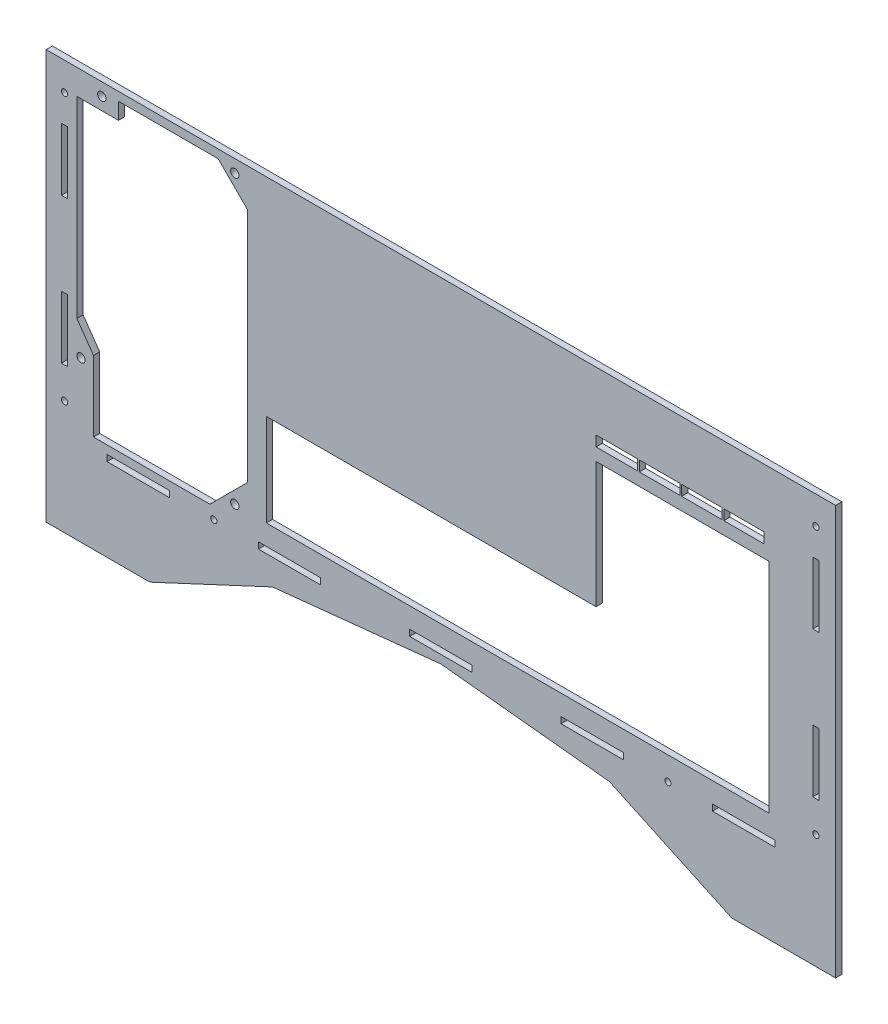
SolidWorks part; units mm, degrees
ref_plane "Front Plane" through (0, 0, 0) normal (0, 0, 1) x (1, 0, 0)
ref_plane "Top Plane" through (0, 0, 0) normal (0, 1, 0) x (1, 0, 0)
ref_plane "Right Plane" through (0, 0, 0) normal (1, 0, 0) x (0, 0, -1)
sketch "Sketch1" plane through (-12.6118, -16.6961, 0) normal (0, 0, 1) x (0, -1, 0)
  line L0 (-209.5933, 95.4118) -> (-195.5933, 109.4118)
  line L1 (-195.5933, 109.4118) -> (-81.5933, 109.4118)
  line L2 (-81.5933, 109.4118) -> (-63.5933, 91.4118)
  line L3 (-63.5933, 91.4118) -> (-63.5933, 35.4118)
  line L4 (-63.5933, 35.4118) -> (-97.5933, 35.4118)
  line L5 (-97.5933, 35.4118) -> (-109.0185, 27.4118)
  line L6 (-109.0185, 27.4118) -> (-201.5933, 27.4118)
  line L7 (-201.5933, 27.4118) -> (-201.5933, 47.4118)
  line L8 (-201.5933, 47.4118) -> (-209.5933, 47.4118)
  line L9 (-209.5933, 47.4118) -> (-209.5933, 95.4118)
  line L10 (-213.6961, 12.6118) -> (-213.6961, 392.6118)
  line L11 (-213.6961, 392.6118) -> (-16.6961, 392.6118)
  line L12 (-16.6961, 392.6118) -> (-16.6961, 342.6118)
  line L13 (-16.6961, 342.6118) -> (-44.1663, 283.7018)
  line L14 (-44.1663, 283.7018) -> (-52.5933, 202.6118)
  line L15 (-52.5933, 202.6118) -> (-44.1663, 121.5218)
  line L16 (-44.1663, 121.5218) -> (-16.6961, 62.6118)
  line L17 (-16.6961, 62.6118) -> (-16.6961, 12.6118)
  line L18 (-16.6961, 12.6118) -> (-213.6961, 12.6118)
  line L19 (-59.5933, 290.4689) -> (-56.5933, 333.3261) construction
  line L20 (-186.6799, 19.9918) -> (-156.6799, 19.9918)
  line L21 (-186.6799, 19.9918) -> (-186.6799, 22.9918)
  line L22 (-186.6799, 22.9918) -> (-156.6799, 22.9918)
  line L23 (-156.6799, 19.9918) -> (-156.6799, 22.9918)
  line L24 (-116.6799, 19.9918) -> (-86.6799, 19.9918)
  line L25 (-116.6799, 19.9918) -> (-116.6799, 22.9918)
  line L26 (-116.6799, 22.9918) -> (-86.6799, 22.9918)
  line L27 (-86.6799, 19.9918) -> (-86.6799, 22.9918)
  line L28 (-59.5933, 41.8975) -> (-56.5933, 41.8975)
  line L29 (-59.5933, 41.8975) -> (-59.5933, 71.8975)
  line L30 (-59.5933, 71.8975) -> (-56.5933, 71.8975)
  line L31 (-56.5933, 41.8975) -> (-56.5933, 71.8975)
  line L32 (-59.5933, 114.7546) -> (-56.5933, 114.7546)
  line L33 (-59.5933, 114.7546) -> (-59.5933, 144.7546)
  line L34 (-59.5933, 144.7546) -> (-56.5933, 144.7546)
  line L35 (-56.5933, 114.7546) -> (-56.5933, 144.7546)
  line L36 (-59.5933, 187.6118) -> (-56.5933, 187.6118)
  line L37 (-59.5933, 187.6118) -> (-59.5933, 217.6118)
  line L38 (-59.5933, 217.6118) -> (-56.5933, 217.6118)
  line L39 (-56.5933, 187.6118) -> (-56.5933, 217.6118)
  line L40 (-59.5933, 260.4689) -> (-56.5933, 260.4689)
  line L41 (-59.5933, 260.4689) -> (-59.5933, 290.4689)
  line L42 (-59.5933, 290.4689) -> (-56.5933, 290.4689)
  line L43 (-56.5933, 260.4689) -> (-56.5933, 290.4689)
  line L44 (-59.5933, 333.3261) -> (-56.5933, 333.3261)
  line L45 (-59.5933, 333.3261) -> (-59.5933, 363.3261)
  line L46 (-59.5933, 363.3261) -> (-56.5933, 363.3261)
  line L47 (-56.5933, 333.3261) -> (-56.5933, 363.3261)
  line L48 (-59.5933, 41.8975) -> (-59.5933, 12.6118) construction
  line L49 (-86.6961, 381.6118) -> (-116.6961, 381.6118)
  line L50 (-86.6961, 381.6118) -> (-86.6961, 384.6118)
  line L51 (-86.6961, 384.6118) -> (-116.6961, 384.6118)
  line L52 (-116.6961, 381.6118) -> (-116.6961, 384.6118)
  line L53 (-186.6961, 381.6118) -> (-156.6961, 381.6118)
  line L54 (-186.6961, 381.6118) -> (-186.6961, 384.6118)
  line L55 (-186.6961, 384.6118) -> (-156.6961, 384.6118)
  line L56 (-156.6961, 381.6118) -> (-156.6961, 384.6118)
  line L57 (-59.5933, 363.3261) -> (-59.5933, 392.6118) construction
  line L58 (-69.3533, 118.5718) -> (-113.8033, 118.5718)
  line L59 (-113.8033, 118.5718) -> (-113.8033, 277.3218)
  line L60 (-113.8033, 277.3218) -> (-174.3533, 277.3218)
  line L61 (-174.3533, 277.3218) -> (-174.3533, 360.5952)
  line L62 (-180.4233, 297.2952) -> (-180.4233, 298.1652) construction
  line L63 (-180.4233, 317.6152) -> (-180.4233, 318.4852) construction
  line L64 (-174.3533, 360.5952) -> (-69.3533, 360.5952)
  line L65 (-180.4233, 337.9352) -> (-180.4233, 338.8052) construction
  line L66 (-69.3533, 360.5952) -> (-69.3533, 118.5718)
  line L67 (-180.4233, 277.3218) -> (-185.4233, 277.3218)
  line L68 (-180.4233, 277.3218) -> (-180.4233, 297.2952)
  line L69 (-180.4233, 297.2952) -> (-185.4233, 297.2952)
  line L70 (-185.4233, 277.3218) -> (-185.4233, 297.2952)
  line L71 (-180.4233, 298.1652) -> (-185.4233, 298.1652)
  line L72 (-180.4233, 298.1652) -> (-180.4233, 317.6152)
  line L73 (-180.4233, 317.6152) -> (-185.4233, 317.6152)
  line L74 (-185.4233, 298.1652) -> (-185.4233, 317.6152)
  line L75 (-180.4233, 318.4852) -> (-185.4233, 318.4852)
  line L76 (-180.4233, 318.4852) -> (-180.4233, 337.9352)
  line L77 (-180.4233, 337.9352) -> (-185.4233, 337.9352)
  line L78 (-185.4233, 318.4852) -> (-185.4233, 337.9352)
  line L79 (-185.4233, 338.8052) -> (-180.4233, 338.8052)
  line L80 (-185.4233, 338.8052) -> (-185.4233, 358.2552)
  line L81 (-185.4233, 358.2552) -> (-180.4233, 358.2552)
  line L82 (-180.4233, 338.8052) -> (-180.4233, 358.2552)
  line L83 (-180.4233, 277.3218) -> (-174.3533, 277.3218) construction
  line L84 (-156.6799, 19.9918) -> (-116.6799, 19.9918) construction
  line L85 (-86.6799, 21.4918) -> (-71.6799, 21.4918) construction
  line L86 (-200.1799, 21.4918) -> (-186.6799, 21.4918) construction
  circle A0 centre (-207.5933, 103.4118) radius 2
  circle A1 centre (-69.5933, 103.4118) radius 2
  circle A2 centre (-93.5933, 29.4118) radius 2
  circle A3 centre (-207.5933, 39.4118) radius 2
  circle A4 centre (-200.1799, 21.4918) radius 1.5
  circle A5 centre (-58.0933, 311.8975) radius 1.5
  circle A6 centre (-200.1961, 383.1118) radius 1.5
  circle A7 centre (-71.6961, 383.1118) radius 1.5
  circle A8 centre (-58.0933, 93.3261) radius 1.5
  circle A9 centre (-71.6799, 21.4918) radius 1.5
  point P100 (0, 0)
  point P102 (0, 0)
  dimension "D1" = 4
  dimension "D44" = 3
  dimension "D53" = 3
  dimension "D54" = 3
  dimension "D55" = 3
  dimension "D92" = 5.5
  dimension "D2" = 2
  dimension "D3" = 6
  dimension "D4" = 2
  dimension "D5" = 12
  dimension "D6" = 2
  dimension "D7" = 30
  dimension "D8" = 6
  dimension "D9" = 6
  dimension "D10" = 19.799
  dimension "D11" = 48
  dimension "D12" = 135
  dimension "D13" = 20
  dimension "D14" = 92.5748
  dimension "D15" = 13.9476
  dimension "D16" = 215
  dimension "D17" = 34
  dimension "D18" = 56
  dimension "D19" = 8
  dimension "D20" = 44.45
  dimension "D21" = 158.75
  dimension "D22" = 242.0234
  dimension "D23" = 105
  dimension "D24" = 19.9734
  dimension "D25" = 5
  dimension "D26" = 5
  dimension "D27" = 19.45
  dimension "D28" = 5
  dimension "D29" = 19.45
  dimension "D30" = 5
  dimension "D31" = 19.45
  dimension "D32" = 0.87
  dimension "D33" = 6.07
  dimension "D34" = 9.16
  dimension "D35" = 9.76
  dimension "D36" = 15
  dimension "D37" = 9.5
  dimension "D38" = 8
  dimension "D39" = 70
  dimension "D40" = 8
  dimension "D41" = 13.5
  dimension "D42" = 9.5
  dimension "D43" = 13.5
  dimension "D45" = 3
  dimension "D46" = 30
  dimension "D47" = 155
  dimension "D48" = 199.067
  dimension "D49" = 168.134
  dimension "D50" = 160.933
  dimension "D51" = 4
  dimension "D52" = 65
  dimension "D56" = 197
  dimension "D57" = 50
  dimension "D58" = 13.5163
  dimension "D60" = 30
  dimension "D61" = 3
  dimension "D62" = 13.5
  dimension "D63" = 40
  dimension "D64" = 3
  dimension "D65" = 30
  dimension "D66" = 7.38
  dimension "D68" = 15
  dimension "D69" = 29.2857
  dimension "D70" = 3
  dimension "D71" = 30
  dimension "D72" = 39.8972
  dimension "D73" = 3
  dimension "D74" = 42.8571
  dimension "D75" = 42.8571
  dimension "D76" = 3
  dimension "D77" = 30
  dimension "D78" = 4.42
  dimension "D79" = 4.1028
  dimension "D80" = 21.4286
  dimension "D81" = 21.4286
  dimension "D82" = 30
  dimension "D83" = 3
  dimension "D84" = 3
  dimension "D85" = 30
  dimension "D86" = 42.8571
  dimension "D88" = 9.76
  dimension "D89" = 9.76
  dimension "D90" = 9.76
  dimension "D91" = 4
extrude "Boss-Extrude1" add sketch "Sketch1" along normal blind 3
